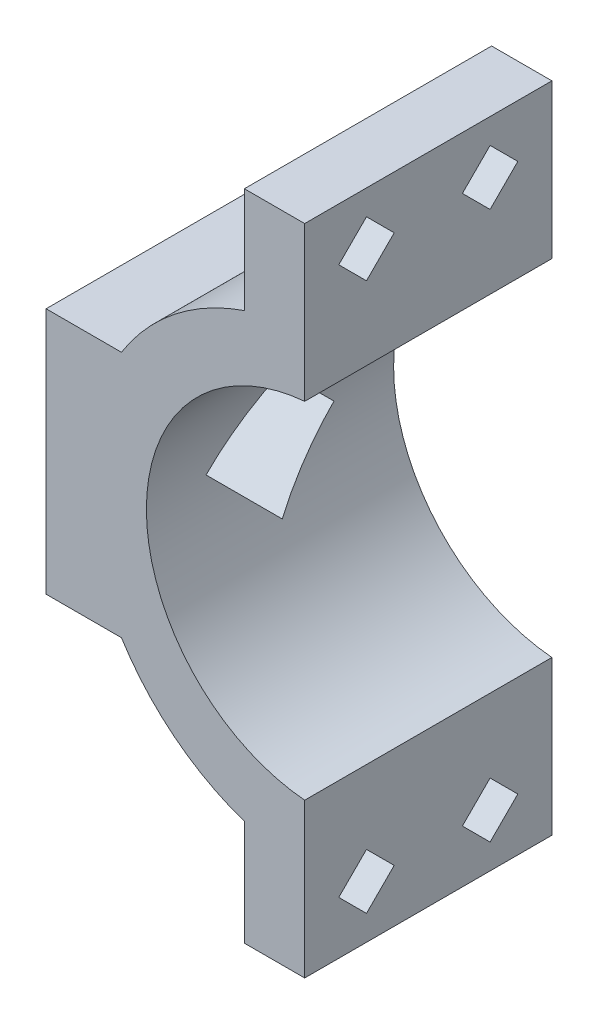
SolidWorks part; units mm, degrees
material "ABS"
ref_plane "Front Plane" through (0, 0, 0) normal (0, 0, 1) x (1, 0, 0)
ref_plane "Top Plane" through (0, 0, 0) normal (0, 1, 0) x (1, 0, 0)
ref_plane "Right Plane" through (0, 0, 0) normal (1, 0, 0) x (0, 0, -1)
sketch "Sketch1" plane through (0, 0, 0) normal (0, 0, 1) x (1, 0, 0)
  line L0 (-1.27, 18.6327) -> (-1.27, 14.5497)
  line L1 (-6.35, 24.7096) -> (-1.27, 24.7096) construction
  line L2 (-1.27, 18.6327) -> (-1.27, 27.5227)
  line L3 (-1.27, 27.5227) -> (-6.35, 27.5227)
  line L4 (-6.35, 27.5227) -> (-6.35, 18.6327)
  line L5 (0, 0) -> (-16.7047, 0) construction
  line L6 (-6.35, 23.0777) -> (-1.27, 23.0777) construction
  line L7 (-6.35, 21.4457) -> (-1.27, 21.4457) construction
  line L8 (-16.7047, 10.414) -> (-23.0547, 10.414)
  line L9 (-23.0547, 10.414) -> (-23.0547, 0)
  line L10 (-23.0547, 0) -> (-14.605, 0)
  arc A0 (-1.27, 14.5497) -> (-14.605, 0) centre (0, 0) ccw
  arc A1 (-6.35, 18.6327) -> (-16.7047, 10.414) centre (0, 0) ccw
  dimension "D1" = 29.21
  dimension "D2" = 5.08
  dimension "D3" = 1.27
  dimension "D4" = 5.08
  dimension "D5" = 8.89
  dimension "D6" = 3.2639
  dimension "D7" = 6.35
  dimension "D8" = 20.828
extrude "Boss-Extrude1" add sketch "Sketch1" along normal mid plane 20.828
mirror "Mirror1" about plane through (-23.0547, 0, 10.414) normal (0, 1, 0) of "Boss-Extrude1"
sketch "Sketch2" plane through (-6.35, 0, 0) normal (-1, 0, 0) x (0, 0, 1)
  line L0 (0, 27.5227) -> (0, -27.5227) construction
  line L1 (10.414, 27.5227) -> (-10.414, 27.5227) construction
  line L2 (10.414, -27.5227) -> (-10.414, -27.5227) construction
  line L3 (5.207, 20.7428) -> (5.207, 25.4125) construction
  line L4 (7.5419, 23.0777) -> (2.8721, 23.0777) construction
  line L5 (5.207, 25.4125) -> (2.8721, 23.0777)
  line L6 (5.207, 20.7428) -> (2.8721, 23.0777)
  line L7 (7.5419, 23.0777) -> (5.207, 25.4125)
  line L8 (7.5419, 23.0777) -> (5.207, 20.7428)
  line L9 (-10.414, 23.0777) -> (10.414, 23.0777) construction
  line L10 (-10.414, 27.5227) -> (-10.414, 18.6327) construction
  line L11 (10.414, 27.5227) -> (10.414, 18.6327) construction
  line L18 (-7.5419, 23.0777) -> (-5.207, 20.7428)
  line L19 (-7.5419, 23.0777) -> (-5.207, 25.4125)
  line L20 (-5.207, 20.7428) -> (-2.8721, 23.0777)
  line L21 (-5.207, 25.4125) -> (-2.8721, 23.0777)
  line L22 (-7.5419, 23.0777) -> (-2.8721, 23.0777) construction
  line L23 (-5.207, 20.7428) -> (-5.207, 25.4125) construction
  point P10 (5.207, 23.0777)
  point P28 (-5.207, 23.0777)
  dimension "D1" = 10.414
  dimension "D2" = 3.302
extrude "Cut-Extrude1" cut sketch "Sketch2" against normal through all
sketch "Sketch5" plane through (-6.35, 0, 0) normal (-1, 0, 0) x (0, 0, 1)
  line L1 (-8.8732, 23.0777) -> (-7.0401, 19.9027)
  line L2 (-7.0401, 19.9027) -> (-3.3739, 19.9027)
  line L3 (-3.3739, 19.9027) -> (-1.5408, 23.0777)
  line L4 (-1.5408, 23.0777) -> (-3.3739, 26.2527)
  line L5 (-3.3739, 26.2527) -> (-7.0401, 26.2527)
  line L6 (-7.0401, 26.2527) -> (-8.8732, 23.0777)
  line L7 (1.5408, 23.0777) -> (3.3739, 19.9027)
  line L8 (3.3739, 19.9027) -> (7.0401, 19.9027)
  line L9 (7.0401, 19.9027) -> (8.8732, 23.0777)
  line L10 (8.8732, 23.0777) -> (7.0401, 26.2527)
  line L11 (7.0401, 26.2527) -> (3.3739, 26.2527)
  line L12 (3.3739, 26.2527) -> (1.5408, 23.0777)
  circle A0 centre (-5.207, 23.0777) radius 3.175 construction
  circle A1 centre (5.207, 23.0777) radius 3.175 construction
  dimension "D1" = 6.35
extrude "Cut-Extrude3" cut sketch "Sketch5" against normal blind 2.3813
mirror "Mirror2" about plane through (0, 0, 0) normal (0, 1, 0) of "Cut-Extrude3", "Cut-Extrude1"
sketch "Sketch3" plane through (-23.0547, 0, 0) normal (-1, 0, 0) x (0, 0, 1)
  line L0 (-10.414, 0) -> (10.414, 0) construction
  line L1 (10.414, 10.414) -> (10.414, -10.414) construction
  line L2 (0, 5.3882) -> (-5.3882, 0)
  line L3 (0, 5.3882) -> (5.3882, 0)
  line L4 (-5.3882, 0) -> (0, -5.3882)
  line L5 (5.3882, 0) -> (0, -5.3882)
  line L6 (0, 5.3882) -> (0, -5.3882) construction
  line L7 (-5.3882, 0) -> (5.3882, 0) construction
  line L8 (-10.414, 10.414) -> (-10.414, -10.414) construction
  circle A0 centre (0, 0) radius 3.81 construction
  dimension "D1" = 7.62
extrude "Cut-Extrude2" cut sketch "Sketch3" against normal through all
sketch "Sketch4" plane through (-23.0547, 0, 0) normal (-1, 0, 0) x (0, 0, 1)
  circle A0 centre (0, 0) radius 5.3882
split line "Split Line1"
